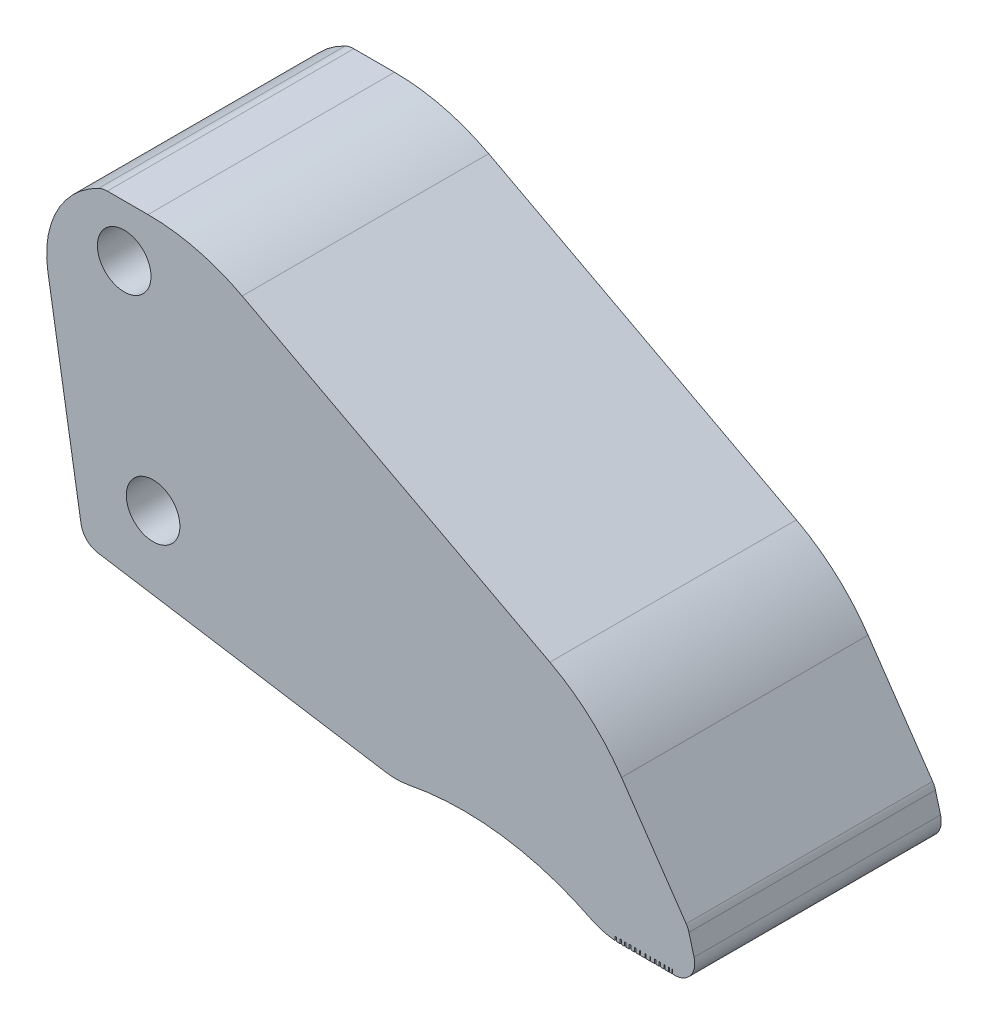
SolidWorks part; units mm, degrees
ref_plane "Front Plane" through (0, 0, 0) normal (0, 0, 1) x (1, 0, 0)
ref_plane "Top Plane" through (0, 0, 0) normal (0, 1, 0) x (1, 0, 0)
ref_plane "Right Plane" through (0, 0, 0) normal (1, 0, 0) x (0, 0, -1)
sketch "Sketch1" plane through (0, 0, 0) normal (0, 0, 1) x (1, 0, 0)
  line L0 (0, 0) -> (42.98, -6.863)
  line L1 (-2.4872, 2.4759) -> (-7.4453, 32.6392)
  line L2 (1.427, 47.4759) -> (7.507, 47.4759)
  line L3 (21.5666, 43.9773) -> (67.5024, 19.6073)
  line L4 (78.2003, 10.049) -> (87.8409, -4.038)
  line L6 (86.1285, -11.5611) -> (78.0585, -11.5611)
  line L7 (89.0249, -7.7795) -> (88.2615, -4.9507)
  line L8 (86.1285, -11.5611) -> (86.1285, -10.9546)
  line L9 (86.1285, -10.9546) -> (76.7105, -10.9546)
  line L10 (76.7105, -10.9546) -> (76.7105, -11.4699)
  line L12 (76.7105, -10.9546) -> (77.1941, -10.9546)
  line L13 (76.7105, -10.9546) -> (76.7105, -11.4699)
  line L15 (77.1941, -10.9546) -> (77.1941, -11.5237)
  line L16 (77.4754, -10.9546) -> (77.982, -10.9546)
  line L17 (77.4754, -10.9546) -> (77.4754, -11.5441)
  line L19 (77.982, -10.9546) -> (77.982, -11.5609)
  line L20 (78.2003, -10.9546) -> (78.6439, -10.9546)
  line L21 (78.2003, -10.9546) -> (78.2003, -11.5611)
  line L22 (78.2003, -11.5611) -> (78.6439, -11.5611)
  line L23 (78.6439, -10.9546) -> (78.6439, -11.5611)
  line L24 (78.8727, -10.9546) -> (79.314, -10.9546)
  line L25 (78.8727, -10.9546) -> (78.8727, -11.5611)
  line L26 (78.8727, -11.5611) -> (79.314, -11.5611)
  line L27 (79.314, -10.9546) -> (79.314, -11.5611)
  line L28 (79.5919, -10.9546) -> (80.1312, -10.9546)
  line L29 (79.5919, -10.9546) -> (79.5919, -11.5611)
  line L30 (79.5919, -11.5611) -> (80.1312, -11.5611)
  line L31 (80.1312, -10.9546) -> (80.1312, -11.5611)
  line L32 (80.3436, -10.9546) -> (80.8912, -10.9546)
  line L33 (80.3436, -10.9546) -> (80.3436, -11.5611)
  line L34 (80.3436, -11.5611) -> (80.8912, -11.5611)
  line L35 (80.8912, -10.9546) -> (80.8912, -11.5611)
  line L36 (81.0137, -10.9546) -> (81.7002, -10.9546)
  line L37 (81.0137, -10.9546) -> (81.0137, -11.5611)
  line L38 (81.0137, -11.5611) -> (81.7002, -11.5611)
  line L39 (81.7002, -10.9546) -> (81.7002, -11.5611)
  line L40 (81.8718, -10.9546) -> (82.4193, -10.9546)
  line L41 (81.8718, -10.9546) -> (81.8718, -11.5611)
  line L42 (81.8718, -11.5611) -> (82.4193, -11.5611)
  line L43 (82.4193, -10.9546) -> (82.4193, -11.5611)
  line L44 (82.5351, -10.9546) -> (83.143, -10.9546)
  line L45 (82.5351, -10.9546) -> (82.5351, -11.5611)
  line L46 (82.5351, -11.5611) -> (83.143, -11.5611)
  line L47 (83.143, -10.9546) -> (83.143, -11.5611)
  line L48 (83.3265, -10.9546) -> (83.7994, -10.9546)
  line L49 (83.3265, -10.9546) -> (83.3265, -11.5611)
  line L50 (83.3265, -11.5611) -> (83.7994, -11.5611)
  line L51 (83.7994, -10.9546) -> (83.7994, -11.5611)
  line L52 (84.0021, -10.9546) -> (84.5039, -10.9546)
  line L53 (84.0021, -10.9546) -> (84.0021, -11.5611)
  line L54 (84.0021, -11.5611) -> (84.5039, -11.5611)
  line L55 (84.5039, -10.9546) -> (84.5039, -11.5611)
  line L56 (84.6776, -10.9546) -> (85.2373, -10.9546)
  line L57 (84.6776, -10.9546) -> (84.6776, -11.5611)
  line L58 (84.6776, -11.5611) -> (85.2373, -11.5611)
  line L59 (85.2373, -10.9546) -> (85.2373, -11.5611)
  line L60 (85.3651, -10.9546) -> (85.7005, -10.9546)
  line L61 (85.3651, -10.9546) -> (85.3651, -11.5611)
  line L62 (85.3651, -11.5611) -> (85.7005, -11.5611)
  line L63 (85.7005, -10.9546) -> (85.7005, -11.5611)
  line L64 (85.8066, -10.9546) -> (86.1285, -10.9546)
  line L65 (85.8066, -10.9546) -> (85.8066, -11.5611)
  line L66 (85.8066, -11.5611) -> (86.1285, -11.5611)
  line L67 (86.1285, -10.9546) -> (86.1285, -11.5611)
  arc A0 (0, 0) -> (-2.4872, 2.4759) centre (0.473, 2.9625) cw
  arc A4 (0.1289, 47.1805) -> (1.427, 47.4759) centre (1.427, 44.4759) cw
  arc A5 (7.507, 47.4759) -> (21.5666, 43.9773) centre (7.507, 17.4759) cw
  arc A6 (67.5024, 19.6073) -> (78.2003, 10.049) centre (53.4428, -6.8941) cw
  arc A7 (87.8409, -4.038) -> (88.2615, -4.9507) centre (85.3651, -5.7323) cw
  arc A8 (89.0249, -7.7795) -> (86.1285, -11.5611) centre (86.1285, -8.5611) cw
  arc A9 (78.0585, -11.5611) -> (73.5869, -10.5057) centre (78.0585, -1.5611) cw
  arc A10 (73.5869, -10.5057) -> (46.4677, -6.8039) centre (54.5869, -48.5109) ccw
  arc A14 (42.98, -6.863) -> (46.4677, -6.8039) centre (44.5568, 3.0119) ccw
  arc A15 (-7.4453, 32.6392) -> (-2.7766, 45.3001) centre (6.0437, 34.8564) cw
  arc A16 (-2.7766, 45.3001) -> (0.1289, 47.1805) centre (6.0437, 34.8564) cw
  circle A17 centre (3.9484, 39.6959) radius 4
  circle A18 centre (8.2675, 9.5617) radius 4
  dimension "D2" = 3
  dimension "D5" = 13.67
  dimension "D6" = 13.67
  dimension "D7" = 3
  dimension "D9" = 30
  dimension "D11" = 30
  dimension "D13" = 3
  dimension "D15" = 3
  dimension "D17" = 10
  dimension "D18" = 42.49
  dimension "D19" = 10
  dimension "D23" = 8
  dimension "D24" = 8
  dimension "D1" = 42.98
  dimension "D8" = 6.08
  dimension "D10" = 52
  dimension "D12" = 17.07
  dimension "D14" = 2.93
  dimension "D16" = 8.07
  dimension "D20" = 37.22
  dimension "D22" = 45
extrude "Boss-Extrude1" add sketch "Sketch1" along normal blind 36.8
ref_plane "Plane1" through (0, -40, 0) normal (0, 1, 0) x (1, 0, 0)
sketch "Sketch2" plane through (0, -40, 0) normal (0, 1, 0) x (1, 0, 0)
  line L0 (46.4677, -36.8) -> (73.5869, -36.8) construction
  line L1 (46.4677, -36.8) -> (73.5869, -36.8)
  line L2 (73.5869, -36.8) -> (73.5869, 0) construction
  line L3 (73.5869, 0) -> (46.4677, 0) construction
  line L4 (46.4677, -36.8) -> (46.4677, 0) construction
  line L5 (73.5869, -36.8) -> (73.5869, 0)
  line L6 (73.5869, 0) -> (46.4677, 0)
  line L7 (46.4677, -36.8) -> (46.4677, 0)
  line L8 (51.4677, -31.8) -> (68.5869, -31.8)
  line L9 (68.5869, -31.8) -> (68.5869, -5)
  line L10 (68.5869, -5) -> (51.4677, -5)
  line L11 (51.4677, -31.8) -> (51.4677, -5)
  dimension "D1" = 5
extrude "Cut-Extrude1" cut sketch "Sketch2" along normal blind 45 contours L11 L8 L9 L10
